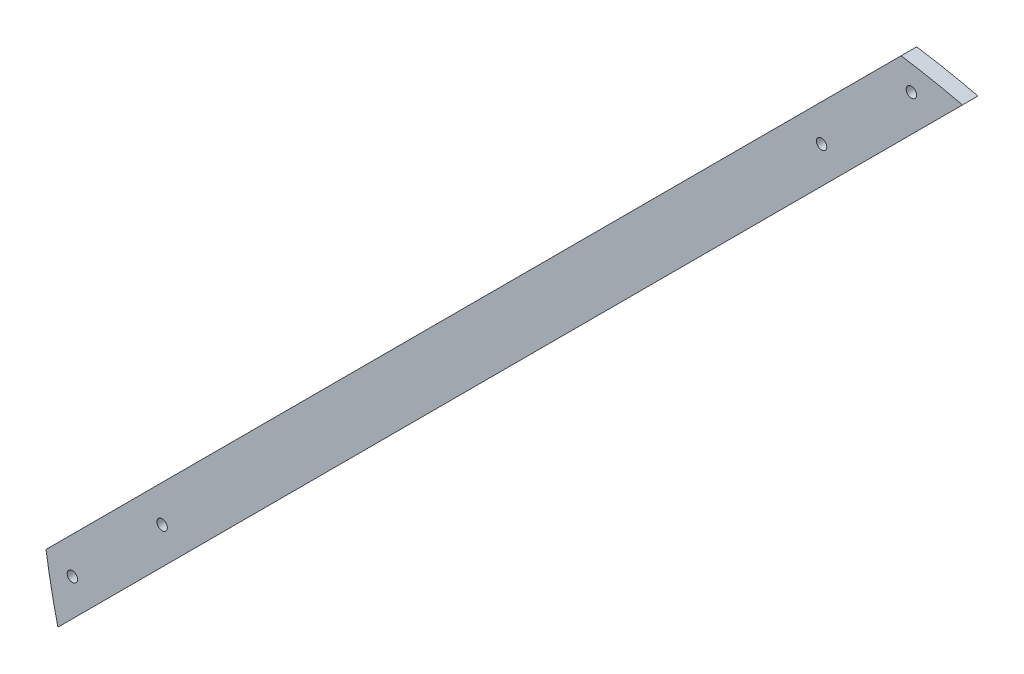
SolidWorks part; units mm, degrees
ref_plane "Plan de face" through (0, 0, 0) normal (0, 0, 1) x (1, 0, 0)
ref_plane "Plan de dessus" through (0, 0, 0) normal (0, 1, 0) x (1, 0, 0)
ref_plane "Plan de droite" through (0, 0, 0) normal (1, 0, 0) x (0, 0, -1)
sketch "Esquisse1" plane through (0, 0, 0) normal (0, 0, 1) x (1, 0, 0)
  line L0 (33.5028, 141.0764) -> (21.2132, 128.7868)
  line L2 (14.1421, 135.8579) -> (21.6577, 143.3734)
  line L3 (-135.8579, -14.1421) -> (14.1421, 135.8579)
  line L5 (-141.0764, -33.5028) -> (-128.7868, -21.2132)
  line L6 (-135.8579, -14.1421) -> (-143.3734, -21.6577)
  line L7 (-128.7868, -21.2132) -> (21.2132, 128.7868)
  arc A0 (21.6577, 143.3734) -> (33.5028, 141.0764) centre (0, 0) cw
  arc A2 (-143.3734, -21.6577) -> (-141.0764, -33.5028) centre (0, 0) ccw
extrude "Boss.-Extru.1" add sketch "Esquisse1" along normal blind 3
sketch "Esquisse2" plane through (0, 0, 3) normal (0, 0, 1) x (1, 0, 0)
  line L0 (0, 0) -> (-102.8013, 102.8013) construction
  line L1 (-141.0764, -33.5028) -> (33.5028, 141.0764) construction
  line L3 (-120.9619, -6.3173) -> (35234.3771, 35349.0218) construction
  circle A0 centre (6.3173, 120.9619) radius 1
  circle A1 centre (-120.9619, -6.3173) radius 1
  circle A2 centre (23.6414, 138.2861) radius 1
  circle A3 centre (-138.2861, -23.6414) radius 1
  dimension "D1" = 180
  dimension "D5" = 229
  dimension "D2" = 90
  dimension "D3" = 5
  dimension "D4" = 5
  dimension "D6" = 114.5
extrude "Enlèv. mat.-Extru.1" cut sketch "Esquisse2" against normal blind 3
